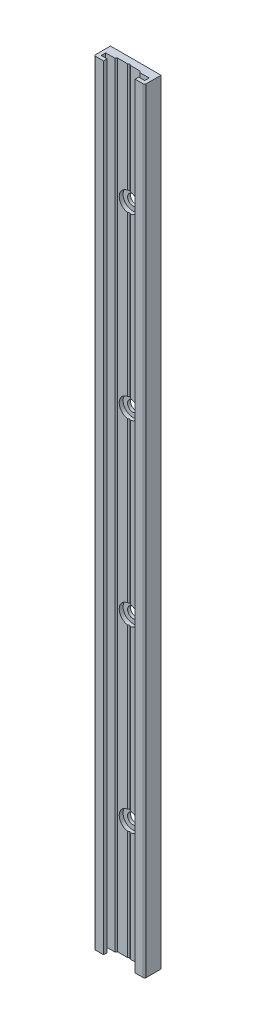
SolidWorks part; units mm, degrees
ref_plane "Front Plane" through (0, 0, 0) normal (0, 0, 1) x (1, 0, 0)
ref_plane "Top Plane" through (0, 0, 0) normal (0, 1, 0) x (1, 0, 0)
ref_plane "Right Plane" through (0, 0, 0) normal (1, 0, 0) x (0, 0, -1)
ref_plane "Plane1" through (0, 0, 5.5) normal (0, 0, 1) x (1, 0, 0)
sketch "Sketch1" plane through (0, 0, 5.5) normal (0, 0, 1) x (1, 0, 0)
  line L0 (-8.5, 0) -> (8.5, 0)
  line L1 (8.5, 0) -> (8.5, 260)
  line L2 (8.5, 260) -> (-8.5, 260)
  line L3 (-8.5, 260) -> (-8.5, 0)
extrude "Boss-Extrude1" add sketch "Sketch1" against normal blind 5.5
sketch "Sketch2" plane through (0, 0, 0) normal (0, -1, 0) x (1, 0, 0)
  line L0 (5.3, 5.5) -> (-5.3, 5.5)
  line L1 (-5.3, 5.5) -> (-5.3, 4.3)
  line L2 (-5.3, 4.3) -> (-7.3, 4.3)
  line L3 (-7.3, 4.3) -> (-7.3, 2.8)
  line L4 (-7.3, 2.8) -> (-4.25, 2.8)
  line L5 (-4.25, 2.8) -> (-4.25, 2.3)
  line L6 (-4.25, 2.3) -> (-0.5, 2.3)
  line L7 (-0.5, 2.3) -> (0.5, 1.7226)
  line L8 (0.5, 1.7226) -> (0.5, 2.3)
  line L9 (0.5, 2.3) -> (3.75, 2.3)
  line L10 (3.75, 2.3) -> (3.75, 2.8)
  line L11 (3.75, 2.8) -> (7.3, 2.8)
  line L12 (7.3, 2.8) -> (7.3, 4.3)
  line L13 (7.3, 4.3) -> (5.3, 4.3)
  line L14 (5.3, 4.3) -> (5.3, 5.5)
extrude "Cut-Extrude1" cut sketch "Sketch2" against normal through all
draft "Draft1" type of draft neutral plane draft angle 45 faces to draft 1 face at (-4.25, 130, 2.55) neutral plane through (-7.3, 260, 2.8) neutral plane normal (0, 0, 1) parameters "D1"=45
draft "Draft2" type of draft neutral plane draft angle 45 faces to draft 1 face at (3.75, 130, 2.55) neutral plane through (0.5, 260, 2.3) neutral plane normal (0, 0, 1) parameters "D1"=45
draft "Draft3" type of draft neutral plane draft angle 60 faces to draft 1 face at (0.5, 130, 2.0113) neutral plane through (0.5, 260, 2.3) neutral plane normal (0, 0, 1) parameters "D1"=60
ref_plane "Plane2" through (0, 160, 0) normal (0, 1, 0) x (1, 0, 0)
sketch "Sketch3" plane through (0, 160, 0) normal (0, 1, 0) x (1, 0, 0)
  line L0 (1.75, 0) -> (0, 0)
  line L1 (0, 0) -> (0, -2.3)
  line L2 (0, -2.3) -> (3.25, -2.3)
  line L3 (3.25, -2.3) -> (3.25, -1)
  line L4 (3.25, -1) -> (1.75, -1)
  line L5 (1.75, -1) -> (1.75, 0)
  line L6 (0, 0) -> (0, -2.3) construction
revolve "Cut-Revolve1" cut sketch "Sketch3" angle 360 about L6
ref_plane "Plane3" through (0, 100, 0) normal (0, 1, 0) x (1, 0, 0)
sketch "Sketch4" plane through (0, 100, 0) normal (0, 1, 0) x (1, 0, 0)
  line L0 (1.75, 0) -> (0, 0)
  line L1 (0, 0) -> (0, -2.3)
  line L2 (0, -2.3) -> (3.25, -2.3)
  line L3 (3.25, -2.3) -> (3.25, -1)
  line L4 (3.25, -1) -> (1.75, -1)
  line L5 (1.75, -1) -> (1.75, 0)
  line L6 (0, 0) -> (0, -2.3) construction
revolve "Cut-Revolve2" cut sketch "Sketch4" angle 360 about L6
ref_plane "Plane4" through (0, 40, 0) normal (0, 1, 0) x (1, 0, 0)
sketch "Sketch5" plane through (0, 40, 0) normal (0, 1, 0) x (1, 0, 0)
  line L0 (1.75, 0) -> (0, 0)
  line L1 (0, 0) -> (0, -2.3)
  line L2 (0, -2.3) -> (3.25, -2.3)
  line L3 (3.25, -2.3) -> (3.25, -1)
  line L4 (3.25, -1) -> (1.75, -1)
  line L5 (1.75, -1) -> (1.75, 0)
  line L6 (0, 0) -> (0, -2.3) construction
revolve "Cut-Revolve3" cut sketch "Sketch5" angle 360 about L6
ref_plane "Plane5" through (0, 220, 0) normal (0, 1, 0) x (1, 0, 0)
sketch "Sketch6" plane through (0, 220, 0) normal (0, 1, 0) x (1, 0, 0)
  line L0 (1.75, 0) -> (0, 0)
  line L1 (0, 0) -> (0, -2.3)
  line L2 (0, -2.3) -> (3.25, -2.3)
  line L3 (3.25, -2.3) -> (3.25, -1)
  line L4 (3.25, -1) -> (1.75, -1)
  line L5 (1.75, -1) -> (1.75, 0)
  line L6 (0, 0) -> (0, -2.3) construction
revolve "Cut-Revolve4" cut sketch "Sketch6" angle 360 about L6
fillet "Fillet1" radius 0.5 2 edges at (-8.5, 130, 5.5) (8.5, 130, 5.5)
